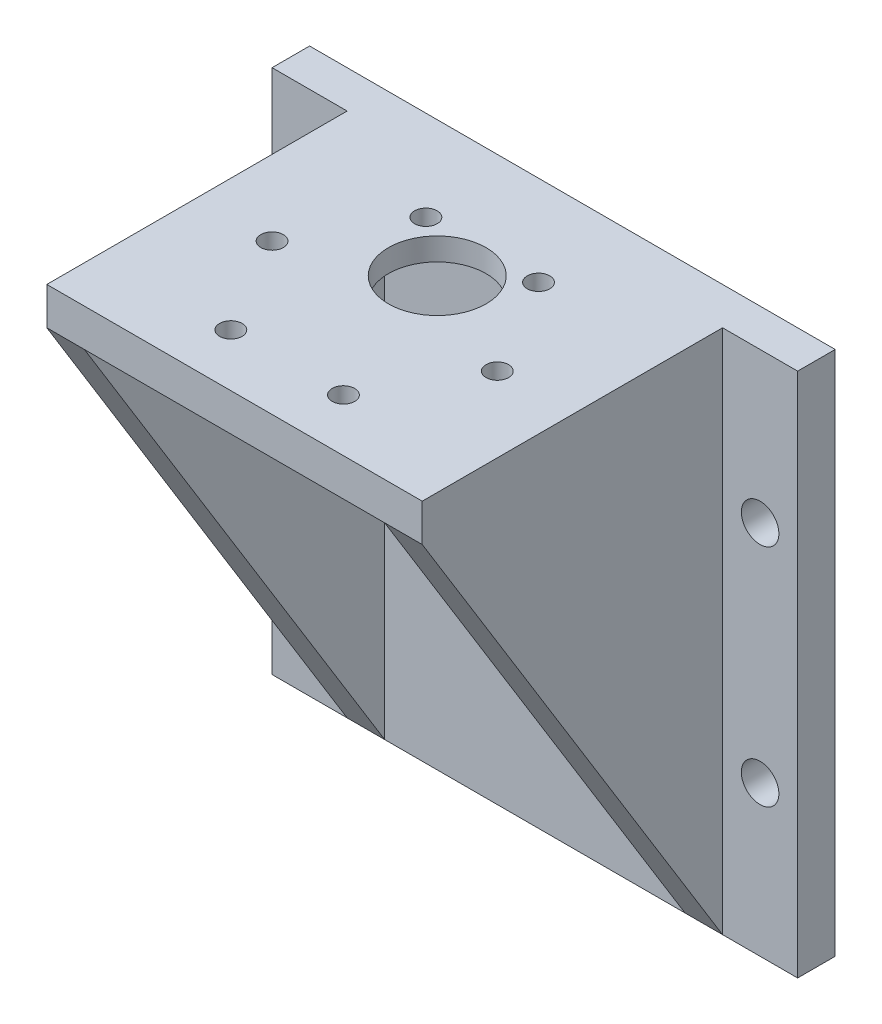
SolidWorks part; units mm, degrees
ref_plane "Plan de face" through (0, 0, 0) normal (0, 0, 1) x (1, 0, 0)
ref_plane "Plan de dessus" through (0, 0, 0) normal (0, 1, 0) x (1, 0, 0)
ref_plane "Plan de droite" through (0, 0, 0) normal (1, 0, 0) x (0, 0, -1)
sketch "Esquisse1" plane through (0, 0, 0) normal (0, 0, 1) x (1, 0, 0)
  line L1 (-46.7149, 33.2769) -> (23.2851, 33.2769)
  line L2 (-46.7149, 33.2769) -> (-46.7149, -36.7231)
  line L3 (-46.7149, -36.7231) -> (23.2851, -36.7231)
  line L4 (23.2851, 33.2769) -> (23.2851, -36.7231)
  dimension "D1" = 70
  dimension "D2" = 70
extrude "Boss.-Extru.1" add sketch "Esquisse1" along normal blind 5
sketch "Esquisse3" plane through (0, 0, 5) normal (0, 0, 1) x (1, 0, 0)
  line L0 (-36.7149, -36.7231) -> (-36.7149, 33.2769)
  line L1 (-46.7149, -36.7231) -> (23.2851, -36.7231) construction
  line L2 (23.2851, 33.2769) -> (-46.7149, 33.2769) construction
  line L3 (-36.7149, 33.2769) -> (13.2851, 33.2769)
  line L4 (13.2851, 33.2769) -> (13.2851, -36.7231)
  line L5 (13.2851, -36.7231) -> (8.2851, -36.7231)
  line L6 (8.2851, -36.7231) -> (8.2851, 28.2769)
  line L7 (8.2851, 28.2769) -> (-31.7149, 28.2769)
  line L8 (-31.7149, 28.2769) -> (-31.7149, -36.7231)
  line L9 (-31.7149, -36.7231) -> (-36.7149, -36.7231)
  line L10 (-46.7149, 33.2769) -> (-46.7149, -36.7231) construction
  line L11 (23.2851, -36.7231) -> (23.2851, 33.2769) construction
  dimension "D1" = 5
  dimension "D2" = 10
  dimension "D3" = 10
  dimension "D4" = 5
  dimension "D5" = 5
extrude "Boss.-Extru.2" add sketch "Esquisse3" along normal blind 40
sketch "Esquisse4" plane through (-36.7149, 0, 0) normal (-1, 0, 0) x (0, 0, 1)
  line L0 (45, 28.2769) -> (5, -36.7231)
  line L1 (45, 33.2769) -> (45, -36.7231) construction
  line L2 (45, -36.7231) -> (5, -36.7231) construction
  line L3 (5, -36.7231) -> (45, -36.7231)
  line L4 (45, -36.7231) -> (45, 28.2769)
  dimension "D1" = 5
extrude "Enlèv. mat.-Extru.1" cut sketch "Esquisse4" against normal up to surface (50 mm away) up to face at (13.2851, -10.4731, 35)
sketch "Esquisse5" plane through (0, 0, 5) normal (0, 0, 1) x (1, 0, 0)
  line L0 (-46.7149, 33.2769) -> (-46.7149, -36.7231) construction
  line L1 (-36.7149, 33.2769) -> (-46.7149, 33.2769) construction
  line L3 (23.2851, -36.7231) -> (23.2851, 33.2769) construction
  line L4 (23.2851, 33.2769) -> (13.2851, 33.2769) construction
  circle A0 centre (-41.7149, 13.2769) radius 2.5
  circle A1 centre (-41.7149, -16.7231) radius 2.5
  circle A2 centre (18.2851, -16.7231) radius 2.5
  circle A3 centre (18.2851, 13.2769) radius 2.5
  dimension "D1" = 5
  dimension "D4" = 5
  dimension "D7" = 5
  dimension "D9" = 5
  dimension "D2" = 5
  dimension "D3" = 20
  dimension "D5" = 5
  dimension "D6" = 20
  dimension "D8" = 5
  dimension "D10" = 30
  dimension "D11" = 30
extrude "Enlèv. mat.-Extru.2" cut sketch "Esquisse5" against normal up to surface (5 mm away) up to face at (-11.7149, -1.7231, 0)
sketch "Esquisse6" plane through (0, 28.2769, 0) normal (0, -1, 0) x (1, 0, 0)
  line L0 (-31.7149, 45) -> (8.2851, 45) construction
  line L1 (-11.7149, 25) -> (-47.5649, 25) construction
  line L3 (-31.7149, 45) -> (-31.7149, 5) construction
  circle A0 centre (-11.7149, 25) radius 19
  dimension "D1" = 38
  dimension "D2" = 20
  dimension "D3" = 20
extrude "Enlèv. mat.-Extru.3" cut sketch "Esquisse6" against normal blind 2
sketch "Esquisse7" plane through (0, 30.2769, 0) normal (0, -1, 0) x (1, 0, 0)
  line L1 (-31.7149, 45) -> (-31.7149, 5) construction
  circle A0 centre (-11.7149, 18) radius 6.5
  circle A1 centre (-11.7149, 25) radius 19 construction
  dimension "D3" = 13
  dimension "D1" = 7
  dimension "D2" = 20
extrude "Enlèv. mat.-Extru.4" cut sketch "Esquisse7" against normal up to surface (3 mm away) up to face at (-10.4649, 33.2769, 18.75)
sketch "Esquisse10" plane through (0, 30.2769, 0) normal (0, -1, 0) x (1, 0, 0)
  line L0 (-40.7757, 25) -> (18.1886, 25) construction
  line L1 (-31.7149, 45) -> (8.2851, 45) construction
  circle A0 centre (-26.7149, 25) radius 1.5
  circle A1 centre (-11.7149, 25) radius 19 construction
  dimension "D2" = 3
  dimension "D3" = 15
  dimension "D1" = 20
extrude "Enlèv. mat.-Extru.5" cut sketch "Esquisse10" against normal up to surface (3 mm away) up to face at (-11.7149, 33.2769, 11.5)
pattern_circular "Répétition circulaire1" count 6 over 360 about axis through (-11.7149, 0, 25) along (0, 1, 0) of "Enlèv. mat.-Extru.5"
